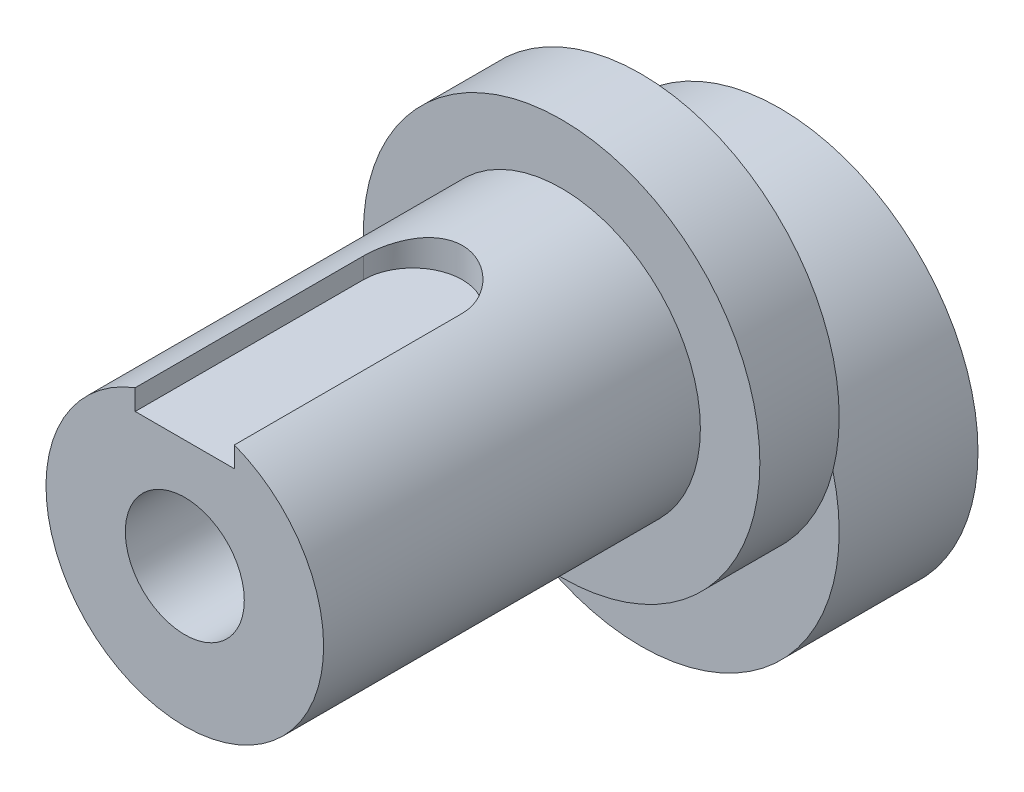
SolidWorks part; units mm, degrees
ref_plane "Front Plane" through (0, 0, 0) normal (0, 0, 1) x (1, 0, 0)
ref_plane "Top Plane" through (0, 0, 0) normal (0, 1, 0) x (1, 0, 0)
ref_plane "Right Plane" through (0, 0, 0) normal (1, 0, 0) x (0, 0, -1)
sketch "Sketch1" plane through (0, 0, 0) normal (0, 0, 1) x (1, 0, 0)
  circle A0 centre (0, 0) radius 10
  circle A1 centre (0, 5) radius 3
  point P5 (0, 0)
  dimension "D1" = 20
  dimension "D2" = 6
  dimension "D3" = 5
extrude "Boss-Extrude1" add sketch "Sketch1" along normal blind 7
sketch "Sketch2" plane through (0, 0, 7) normal (0, 0, 1) x (1, 0, 0)
  circle A0 centre (0, 5) radius 10
  circle A1 centre (0, 5) radius 3 construction
  circle A2 centre (0, 5) radius 3
  dimension "D1" = 20
extrude "Boss-Extrude2" add sketch "Sketch2" along normal blind 4
sketch "Sketch3" plane through (0, 0, 11) normal (0, 0, 1) x (1, 0, 0)
  circle A0 centre (0, 5) radius 7
  circle A1 centre (0, 5) radius 3 construction
  circle A2 centre (0, 5) radius 3
  dimension "D1" = 14
extrude "Boss-Extrude3" add sketch "Sketch3" along normal blind 19
sketch "Sketch5" plane through (0, 0, 0) normal (0, 1, 0) x (1, 0, 0)
  line L0 (-7, -30) -> (7, -30) construction
  line L1 (2.5, -44) -> (-2.5, -44)
  line L2 (2.5, -44) -> (2.5, -18.5)
  line L4 (-2.5, -44) -> (-2.5, -18.5)
  line L5 (2.5, -44) -> (0, -30) construction
  line L7 (0, -30) -> (-2.5, -44) construction
  arc A0 (2.5, -18.5) -> (-2.5, -18.5) centre (0, -18.5) ccw
  point P0 (0, -30)
extrude "Cut-Extrude1" cut sketch "Sketch5" against normal blind 10 from offset 20.5
